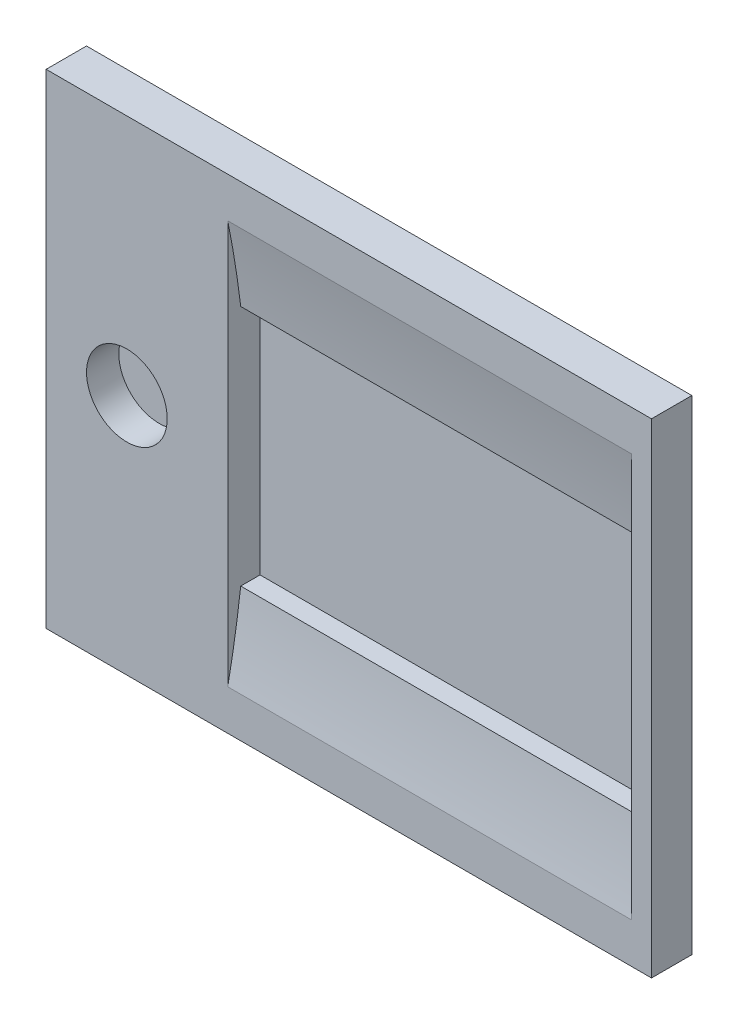
SolidWorks part; units mm, degrees
material "ABS PC"
ref_plane "Front Plane" through (0, 0, 0) normal (0, 0, 1) x (1, 0, 0)
ref_plane "Top Plane" through (0, 0, 0) normal (0, 1, 0) x (1, 0, 0)
ref_plane "Right Plane" through (0, 0, 0) normal (1, 0, 0) x (0, 0, -1)
sketch "Sketch1" plane through (0, 0, 0) normal (0, 0, 1) x (1, 0, 0)
  line L1 (-23.8125, -19.05) -> (23.8125, -19.05)
  line L2 (-23.8125, -19.05) -> (-23.8125, 19.05)
  line L3 (-23.8125, 19.05) -> (23.8125, 19.05)
  line L4 (23.8125, -19.05) -> (23.8125, 19.05)
  line L5 (-23.8125, -19.05) -> (23.8125, 19.05) construction
  line L6 (-23.8125, 19.05) -> (23.8125, -19.05) construction
  point P0 (0, 0)
  dimension "D1" = 47.625
  dimension "D2" = 38.1
extrude "Boss-Extrude1" add sketch "Sketch1" along normal mid plane 3.175
sketch "Sketch2" plane through (0, 0, 1.5875) normal (0, 0, 1) x (1, 0, 0)
  line L0 (-23.8125, 19.05) -> (-23.8125, -19.05) construction
  line L2 (-9.525, -15.875) -> (22.225, -15.875)
  line L3 (-9.525, -15.875) -> (-9.525, 15.875)
  line L4 (-9.525, 15.875) -> (22.225, 15.875)
  line L5 (22.225, -15.875) -> (22.225, 15.875)
  line L6 (-9.525, -15.875) -> (22.225, 15.875) construction
  line L7 (-9.525, 15.875) -> (22.225, -15.875) construction
  line L8 (-9.525, -9.525) -> (22.225, -9.525)
  line L9 (-9.525, -9.525) -> (-9.525, 9.525)
  line L10 (-9.525, 9.525) -> (22.225, 9.525)
  line L11 (22.225, -9.525) -> (22.225, 9.525)
  line L12 (-9.525, -9.525) -> (22.225, 9.525) construction
  line L13 (-9.525, 9.525) -> (22.225, -9.525) construction
  circle A0 centre (-17.4625, 0) radius 3.175
  point P6 (6.35, 0)
  point P12 (6.35, 0)
  dimension "D1" = 6.35
  dimension "D2" = 6.35
  dimension "D3" = 31.75
  dimension "D4" = 31.75
  dimension "D5" = 6.35
  dimension "D6" = 19.05
  dimension "D7" = 31.75
extrude "Cut-Extrude1" cut sketch "Sketch2" against normal blind 2.54 contours L10 L3 L8 L5 | A0
sketch "Sketch4" plane through (23.8125, 0, 0) normal (1, 0, 0) x (0, 0, -1)
  line L0 (-1.5875, -19.05) -> (-1.5875, 19.05) construction
  line L1 (-1.5875, 15.875) -> (0, 15.875)
  line L2 (-1.5875, 15.875) -> (-1.5875, -15.875)
  line L3 (-1.5875, -15.875) -> (0, -15.875)
  line L4 (0, 15.875) -> (0, -15.875)
  arc A0 (-1.5875, -15.875) -> (-1.5875, 15.875) centre (-80.1687, 0) ccw
  spline S0 degree 1 poles (-1.5875, -15.875) (-1.5875, 15.875) knots 0 0 1 1
  point P6 (0, 0)
  line M7 (-1.5875, 19.05) -> (-1.5875, -19.05)
  dimension "D1" = 31.75
  dimension "D2" = 1.5875
extrude "Cut-Extrude2" cut sketch "Sketch4" against normal up to surface (31.75 mm away) from surface at -1.5875 contours A0 M7 up to face at (-9.525, 0, 0.3175) starting at face at (22.225, 0, 0.3175)
